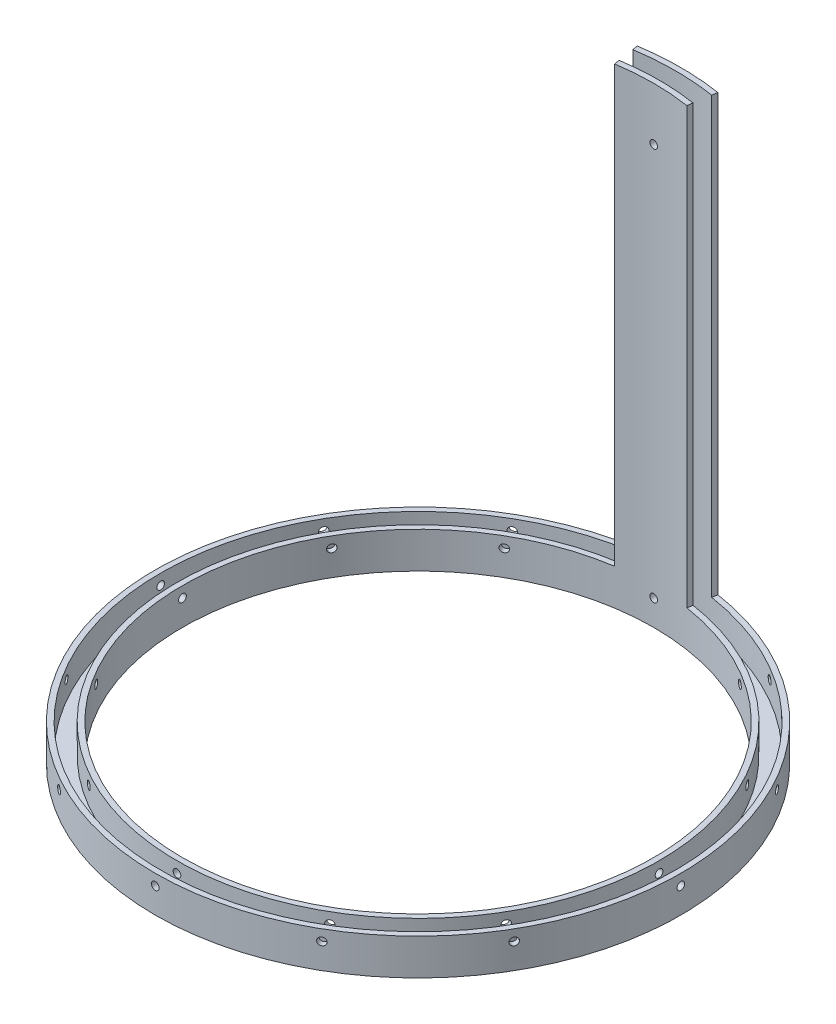
SolidWorks part; units mm, degrees
ref_plane "Front Plane" through (0, 0, 0) normal (0, 0, 1) x (1, 0, 0)
ref_plane "Top Plane" through (0, 0, 0) normal (0, 1, 0) x (1, 0, 0)
ref_plane "Right Plane" through (0, 0, 0) normal (1, 0, 0) x (0, 0, -1)
sketch "Sketch1" plane through (0, 0, 0) normal (0, 1, 0) x (1, 0, 0)
  circle A0 centre (0, 0) radius 92.075
  circle A1 centre (0, 0) radius 82.55
  dimension "D1" = 184.15
  dimension "D2" = 165.1
extrude "Boss-Extrude1" add sketch "Sketch1" along normal blind 12.7
sketch "Sketch3" plane through (0, 0, 0) normal (0, 0, 1) x (1, 0, 0)
  line L0 (92.075, 12.7) -> (-92.075, 12.7) construction
  circle A0 centre (0, 8.89) radius 1.3525
  dimension "D1" = 2.7051
  dimension "D2" = 3.81
extrude "Cut-Extrude2" cut sketch "Sketch3" against normal up to surface (92.0651 mm away)
pattern_circular "CirPattern1" count 12 over 360 about axis through (0, 12.7, 0) along (0, 1, 0) of "Cut-Extrude2"
sketch "Sketch4" plane through (0, 12.7, 0) normal (0, 1, 0) x (1, 0, 0)
  line L0 (-12.7, 81.5672) -> (-14.1654, 90.9788)
  line L1 (12.5999, 81.5827) -> (14.0538, 90.9961)
  line L2 (0, 0) -> (-12.7, 81.5672) construction
  arc A0 (-14.1654, 90.9788) -> (14.0538, 90.9961) centre (0, 0) cw
  circle A1 centre (0, 0) radius 92.075 construction
  arc A2 (-12.7, 81.5672) -> (12.5999, 81.5827) centre (0, 0) cw
  circle A4 centre (0, 0) radius 82.55 construction
  point P8 (0, 0)
  dimension "D2" = 25.4
  dimension "D1" = 12.7
extrude "Boss-Extrude2" add sketch "Sketch4" along normal blind 152.4
pattern_linear "LPattern1" count 2 spacing 137.668 along (0, 1, 0) of "Cut-Extrude2"
sketch "Sketch2" plane through (0, 12.7, 0) normal (0, 1, 0) x (1, 0, 0)
  circle A0 centre (0, 0) radius 84.455
  circle A1 centre (0, 0) radius 90.17
  dimension "D1" = 180.34
  dimension "D2" = 168.91
extrude "Cut-Extrude1" cut sketch "Sketch2" against normal blind 10.16 and the other way up to surface
